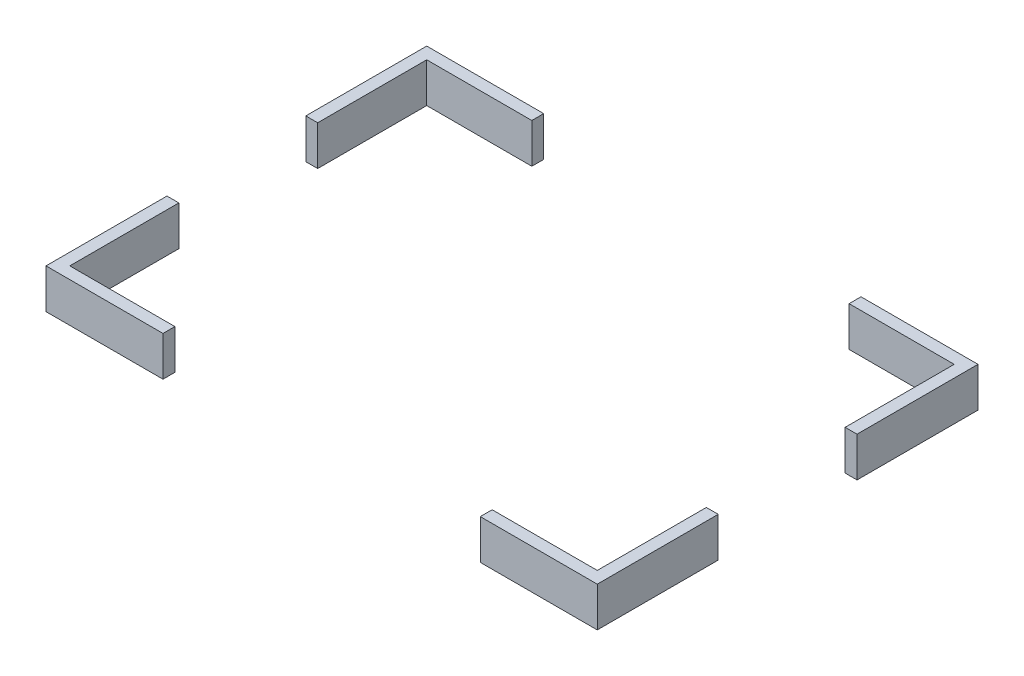
SolidWorks part; units mm, degrees
ref_plane "Front Plane" through (0, 0, 0) normal (0, 0, 1) x (1, 0, 0)
ref_plane "Top Plane" through (0, 0, 0) normal (0, 1, 0) x (1, 0, 0)
ref_plane "Right Plane" through (0, 0, 0) normal (1, 0, 0) x (0, 0, -1)
sketch "Sketch1" plane through (0, 0, 0) normal (0, 1, 0) x (1, 0, 0)
  line L1 (-66.5, 45) -> (66.5, 45)
  line L2 (-66.5, 45) -> (-66.5, -45)
  line L3 (-66.5, -45) -> (66.5, -45)
  line L4 (66.5, 45) -> (66.5, -45)
  line L5 (-69.5, 48) -> (69.5, 48)
  line L6 (-69.5, 48) -> (-69.5, -48)
  line L7 (-69.5, -48) -> (69.5, -48)
  line L8 (69.5, 48) -> (69.5, -48)
  point P4 (0, 0)
  point P5 (0, 0)
  point P6 (0, 0)
  point P7 (0, 0)
extrude "Boss-Extrude1" add sketch "Sketch1" along normal blind 10
sketch "Sketch2" plane through (69.5, 0, 0) normal (1, 0, 0) x (0, 0, -1)
  line L1 (-17.5, 15) -> (17.5, 15)
  line L2 (-17.5, 15) -> (-17.5, -15)
  line L3 (-17.5, -15) -> (17.5, -15)
  line L4 (17.5, 15) -> (17.5, -15)
extrude "Cut-Extrude1" cut sketch "Sketch2" against normal blind 600
sketch "Sketch3" plane through (0, 10, 0) normal (0, 1, 0) x (1, 0, 0)
  line L1 (-40, 58.8496) -> (40, 58.8496)
  line L2 (-40, 58.8496) -> (-40, -61.7558)
  line L3 (-40, -61.7558) -> (40, -61.7558)
  line L4 (40, 58.8496) -> (40, -61.7558)
extrude "Cut-Extrude2" cut sketch "Sketch3" against normal blind 50
